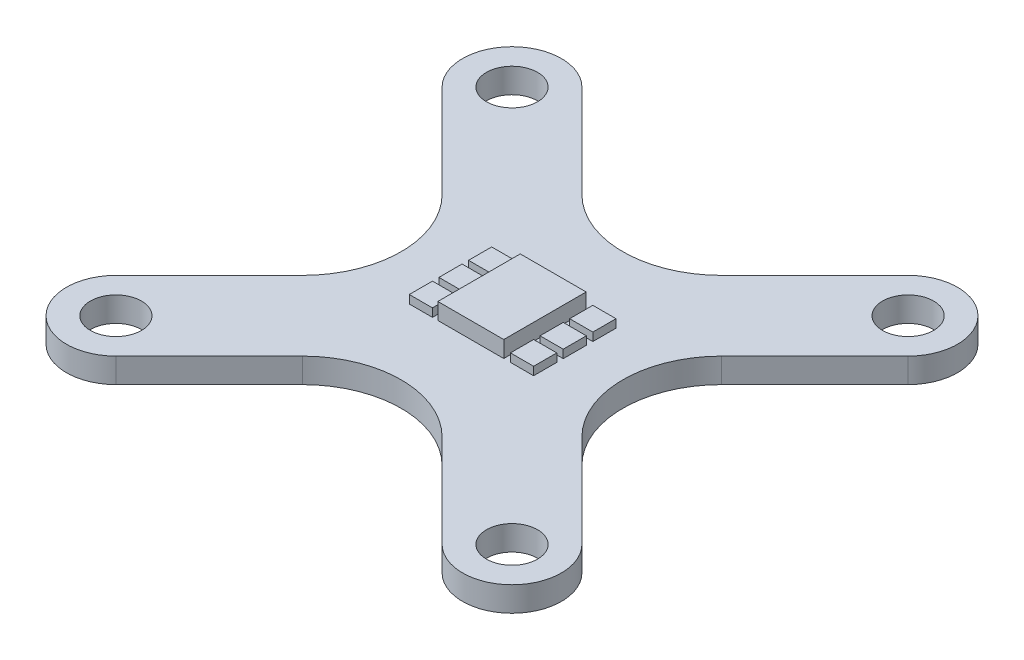
SolidWorks part; units mm, degrees
ref_plane "Front Plane" through (0, 0, 0) normal (0, 0, 1) x (1, 0, 0)
ref_plane "Top Plane" through (0, 0, 0) normal (0, 1, 0) x (1, 0, 0)
ref_plane "Right Plane" through (0, 0, 0) normal (1, 0, 0) x (0, 0, -1)
sketch "Sketch1" plane through (0, 0, 0) normal (0, 1, 0) x (1, 0, 0)
  line L0 (-12.02, -12.02) -> (12.02, 12.02) construction
  line L1 (12.02, -12.02) -> (-12.02, -12.02) construction
  line L2 (12.02, -12.02) -> (12.02, 12.02) construction
  line L3 (12.02, 12.02) -> (-12.02, 12.02) construction
  line L4 (-12.02, -12.02) -> (-12.02, 12.02) construction
  line L5 (12.02, -12.02) -> (-12.02, 12.02) construction
  line L6 (12.02, 12.02) -> (-12.02, -12.02) construction
  line L7 (-14.1413, -9.8987) -> (9.8987, 14.1413)
  line L8 (-9.8987, -14.1413) -> (14.1413, 9.8987)
  line L9 (12.02, -12.02) -> (-12.02, 12.02) construction
  line L10 (9.8987, -14.1413) -> (-14.1413, 9.8987)
  line L11 (14.1413, -9.8987) -> (-9.8987, 14.1413)
  circle A0 centre (-12.02, 12.02) radius 1.55
  circle A1 centre (-12.02, -12.02) radius 1.55
  circle A2 centre (12.02, -12.02) radius 1.55
  circle A3 centre (12.02, 12.02) radius 1.55
  arc A4 (-14.1413, -9.8987) -> (-9.8987, -14.1413) centre (-12.02, -12.02) ccw
  arc A5 (14.1413, 9.8987) -> (9.8987, 14.1413) centre (12.02, 12.02) ccw
  arc A6 (9.8987, -14.1413) -> (14.1413, -9.8987) centre (12.02, -12.02) ccw
  arc A7 (-9.8987, 14.1413) -> (-14.1413, 9.8987) centre (-12.02, 12.02) ccw
  point P0 (0, 0)
  point P10 (0, 0)
  point P15 (0, 0)
  dimension "D1" = 3.1
  dimension "D2" = 24.04
  dimension "D3" = 6
extrude "Boss-Extrude1" add sketch "Sketch1" along normal blind 1.5 contours L8 A5 L7 L11 A3 | L11 A7 L10 L7 A0 | L8 L11 L7 L10 | L10 A6 L11 L8 A2 | L7 A4 L8 L10 A1
fillet "Fillet1" radius 6 4 edges at (-4.2426, 0.75, 0) (0, 0.75, -4.2426) (4.2426, 0.75, 0) (0, 0.75, 4.2426)
sketch "Sketch2" plane through (0, 1.5, 0) normal (0, 1, 0) x (1, 0, 0)
  line L1 (2, -2.5) -> (-2, -2.5)
  line L2 (2, -2.5) -> (2, 2.5)
  line L3 (2, 2.5) -> (-2, 2.5)
  line L4 (-2, -2.5) -> (-2, 2.5)
  line L5 (2, -2.5) -> (-2, 2.5) construction
  line L6 (2, 2.5) -> (-2, -2.5) construction
  point P0 (0, 0)
  dimension "D1" = 5
  dimension "D2" = 4
extrude "Boss-Extrude2" add sketch "Sketch2" along normal blind 1
sketch "Sketch3" plane through (0, 1.5, 0) normal (0, 1, 0) x (1, 0, 0)
  line L0 (-2, -2.5) -> (2, -2.5) construction
  line L1 (-2.3276, -2.5) -> (-3.7332, -2.5)
  line L2 (-2.3276, -2.5) -> (-2.3276, -1.0944)
  line L3 (-2.3276, -1.0944) -> (-3.7332, -1.0944)
  line L4 (-3.7332, -2.5) -> (-3.7332, -1.0944)
  line L5 (-2.3276, -2.5) -> (-3.7332, -1.0944) construction
  line L6 (-2.3276, -1.0944) -> (-3.7332, -2.5) construction
  line L7 (-2.3276, -0.7028) -> (-3.7332, -0.7028)
  line L8 (-2.3276, -0.7028) -> (-2.3276, 0.7028)
  line L9 (-2.3276, 0.7028) -> (-3.7332, 0.7028)
  line L10 (-3.7332, -0.7028) -> (-3.7332, 0.7028)
  line L11 (-2.3276, -0.7028) -> (-3.7332, 0.7028) construction
  line L12 (-2.3276, 0.7028) -> (-3.7332, -0.7028) construction
  line L13 (-2.3276, 1.0944) -> (-3.7332, 1.0944)
  line L14 (-2.3276, 1.0944) -> (-2.3276, 2.5)
  line L15 (-2.3276, 2.5) -> (-3.7332, 2.5)
  line L16 (-3.7332, 1.0944) -> (-3.7332, 2.5)
  line L17 (-2.3276, 1.0944) -> (-3.7332, 2.5) construction
  line L18 (-2.3276, 2.5) -> (-3.7332, 1.0944) construction
  line L19 (3.8109, -0.7028) -> (2.4053, -0.7028)
  line L20 (3.8109, -0.7028) -> (3.8109, 0.7028)
  line L21 (3.8109, 0.7028) -> (2.4053, 0.7028)
  line L22 (2.4053, -0.7028) -> (2.4053, 0.7028)
  line L23 (3.8109, -0.7028) -> (2.4053, 0.7028) construction
  line L24 (3.8109, 0.7028) -> (2.4053, -0.7028) construction
  line L25 (3.8109, -2.5) -> (2.4053, -2.5)
  line L26 (3.8109, -2.5) -> (3.8109, -1.0944)
  line L27 (3.8109, -1.0944) -> (2.4053, -1.0944)
  line L28 (2.4053, -2.5) -> (2.4053, -1.0944)
  line L29 (3.8109, -2.5) -> (2.4053, -1.0944) construction
  line L30 (3.8109, -1.0944) -> (2.4053, -2.5) construction
  line L31 (3.8109, 1.0944) -> (2.4053, 1.0944)
  line L32 (3.8109, 1.0944) -> (3.8109, 2.5)
  line L33 (3.8109, 2.5) -> (2.4053, 2.5)
  line L34 (2.4053, 1.0944) -> (2.4053, 2.5)
  line L35 (3.8109, 1.0944) -> (2.4053, 2.5) construction
  line L36 (3.8109, 2.5) -> (2.4053, 1.0944) construction
  line L37 (2, 2.5) -> (-2, 2.5) construction
  point P0 (-3.0304, -1.7972)
  point P5 (-3.0304, 0)
  point P10 (-3.0304, 1.7972)
  point P15 (3.1081, 0)
  point P20 (3.1081, -1.7972)
  point P25 (3.1081, 1.7972)
  point P30 (0, 0)
  point P31 (0, 0)
  point P32 (0, 0)
  point P34 (0, 0)
  point P35 (0, 0)
  point P40 (0, 0)
  point P41 (0, 0)
  point P42 (0, 0)
extrude "Boss-Extrude3" add sketch "Sketch3" along normal blind 0.5
